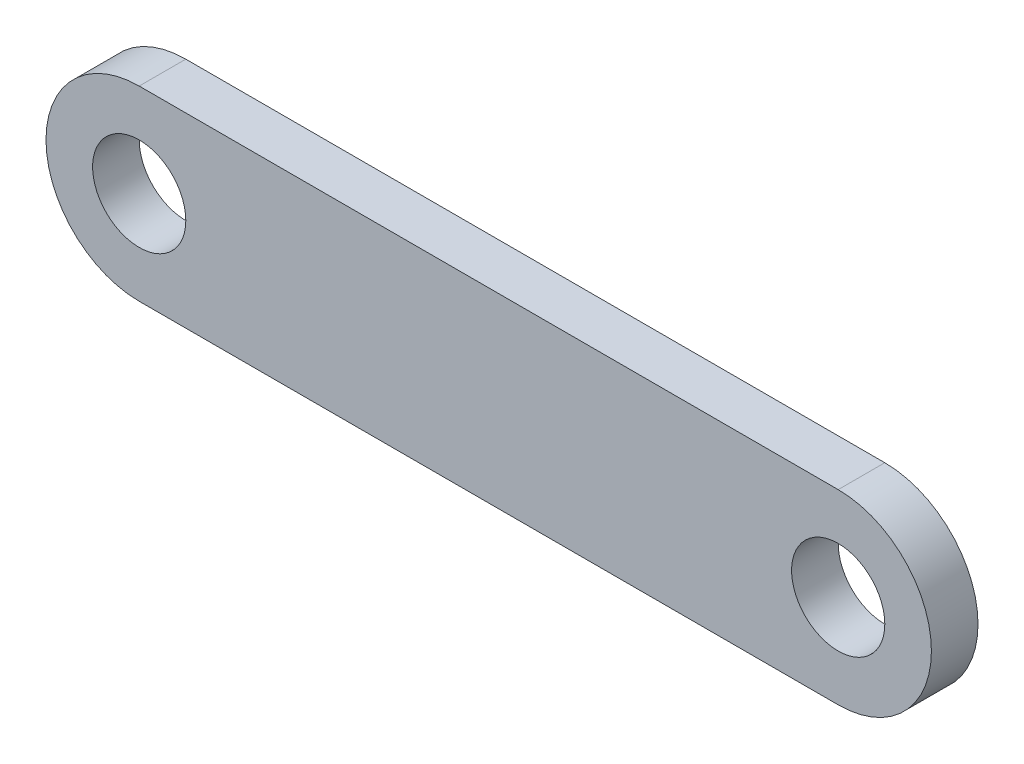
SolidWorks part; units mm, degrees
ref_plane "Front Plane" through (0, 0, 0) normal (0, 0, 1) x (1, 0, 0)
ref_plane "Top Plane" through (0, 0, 0) normal (0, 1, 0) x (1, 0, 0)
ref_plane "Right Plane" through (0, 0, 0) normal (1, 0, 0) x (0, 0, -1)
sketch "Sketch1" plane through (0, 0, 0) normal (0, 0, 1) x (1, 0, 0)
  line L0 (0, 0) -> (38.1, 0) construction
  line L1 (0, 5.08) -> (38.1, 5.08)
  line L2 (0, -5.08) -> (38.1, -5.08)
  arc A0 (0, 5.08) -> (0, -5.08) centre (0, 0) ccw
  arc A1 (38.1, -5.08) -> (38.1, 5.08) centre (38.1, 0) ccw
  circle A2 centre (0, 0) radius 2.54
  circle A3 centre (38.1, 0) radius 2.54
  point P3 (19.05, 0)
  dimension "D2" = 5.08
  dimension "D3" = 5.08
  dimension "D4" = 5.08
  dimension "D1" = 38.1
extrude "Boss-Extrude1" add sketch "Sketch1" along normal blind 2.54
